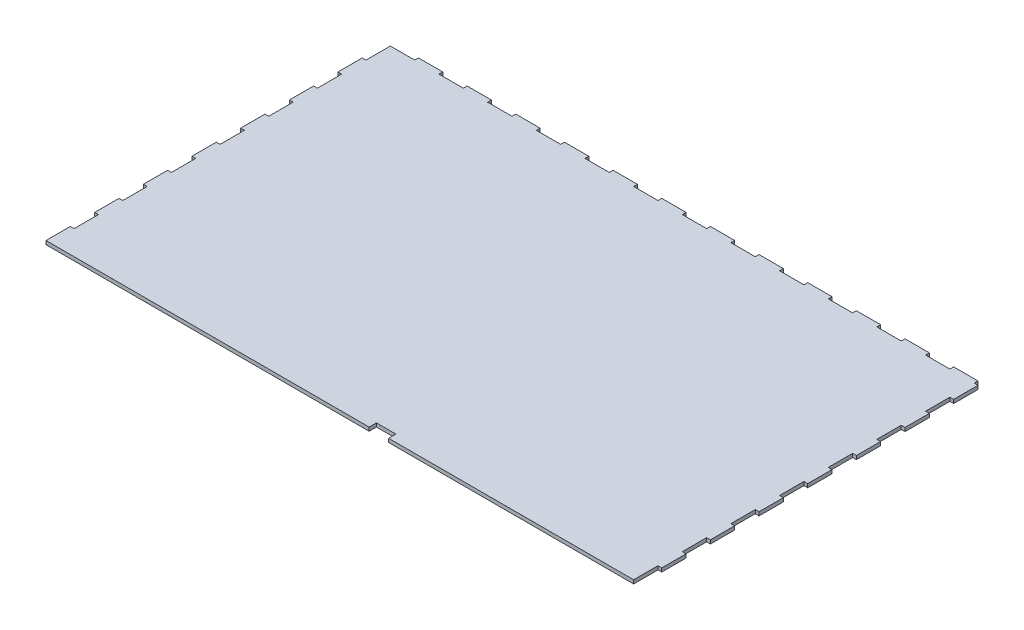
SolidWorks part; units mm, degrees
material "Acrílico (Impacto medio-alto)"
ref_plane "Alzado" through (0, 0, 0) normal (0, 0, 1) x (1, 0, 0)
ref_plane "Planta" through (0, 0, 0) normal (0, 1, 0) x (1, 0, 0)
ref_plane "Vista lateral" through (0, 0, 0) normal (1, 0, 0) x (0, 0, -1)
sketch "Croquis1" plane through (0, 0, 0) normal (0, 1, 0) x (1, 0, 0)
  line L0 (480, 280) -> (480, 283.1)
  line L1 (0, 0) -> (480, 0)
  line L2 (0, 0) -> (0, 280) construction
  line L3 (0, 280) -> (480, 280) construction
  line L4 (480, 0) -> (480, 280) construction
  line L5 (480, 283.1) -> (460, 283.1)
  line L6 (460, 283.1) -> (460, 280)
  line L7 (460, 280) -> (440, 280)
  line L8 (420, 280) -> (400, 280)
  line L9 (420, 283.1) -> (420, 280)
  line L10 (440, 283.1) -> (420, 283.1)
  line L11 (440, 280) -> (440, 283.1)
  line L12 (380, 280) -> (360, 280)
  line L13 (380, 283.1) -> (380, 280)
  line L14 (400, 283.1) -> (380, 283.1)
  line L15 (400, 280) -> (400, 283.1)
  line L16 (340, 280) -> (320, 280)
  line L17 (340, 283.1) -> (340, 280)
  line L18 (360, 283.1) -> (340, 283.1)
  line L19 (360, 280) -> (360, 283.1)
  line L20 (300, 280) -> (280, 280)
  line L21 (300, 283.1) -> (300, 280)
  line L22 (320, 283.1) -> (300, 283.1)
  line L23 (320, 280) -> (320, 283.1)
  line L24 (260, 280) -> (240, 280)
  line L25 (260, 283.1) -> (260, 280)
  line L26 (280, 283.1) -> (260, 283.1)
  line L27 (280, 280) -> (280, 283.1)
  line L28 (220, 280) -> (200, 280)
  line L29 (220, 283.1) -> (220, 280)
  line L30 (240, 283.1) -> (220, 283.1)
  line L31 (240, 280) -> (240, 283.1)
  line L32 (180, 280) -> (160, 280)
  line L33 (180, 283.1) -> (180, 280)
  line L34 (200, 283.1) -> (180, 283.1)
  line L35 (200, 280) -> (200, 283.1)
  line L36 (140, 280) -> (120, 280)
  line L37 (140, 283.1) -> (140, 280)
  line L38 (160, 283.1) -> (140, 283.1)
  line L39 (160, 280) -> (160, 283.1)
  line L40 (100, 280) -> (80, 280)
  line L41 (100, 283.1) -> (100, 280)
  line L42 (120, 283.1) -> (100, 283.1)
  line L43 (120, 280) -> (120, 283.1)
  line L44 (60, 280) -> (40, 280)
  line L45 (60, 283.1) -> (60, 280)
  line L46 (80, 283.1) -> (60, 283.1)
  line L47 (80, 280) -> (80, 283.1)
  line L48 (20, 280) -> (0, 280)
  line L49 (20, 283.1) -> (20, 280)
  line L50 (40, 283.1) -> (20, 283.1)
  line L51 (40, 280) -> (40, 283.1)
  line L52 (480, 280) -> (483.1, 280)
  line L53 (483.1, 280) -> (483.1, 260)
  line L54 (483.1, 260) -> (480, 260)
  line L55 (480, 260) -> (480, 240)
  line L56 (480, 240) -> (483.1, 240)
  line L57 (483.1, 240) -> (483.1, 220)
  line L58 (483.1, 220) -> (480, 220)
  line L59 (480, 220) -> (480, 200)
  line L60 (480, 200) -> (483.1, 200)
  line L61 (483.1, 200) -> (483.1, 180)
  line L62 (483.1, 180) -> (480, 180)
  line L63 (480, 180) -> (480, 160)
  line L64 (480, 160) -> (483.1, 160)
  line L65 (483.1, 160) -> (483.1, 140)
  line L66 (483.1, 140) -> (480, 140)
  line L67 (480, 140) -> (480, 120)
  line L68 (480, 120) -> (483.1, 120)
  line L69 (483.1, 120) -> (483.1, 100)
  line L70 (483.1, 100) -> (480, 100)
  line L71 (480, 100) -> (480, 80)
  line L72 (480, 80) -> (483.1, 80)
  line L73 (483.1, 80) -> (483.1, 60)
  line L74 (483.1, 60) -> (480, 60)
  line L75 (480, 60) -> (480, 40)
  line L76 (480, 40) -> (483.1, 40)
  line L77 (483.1, 40) -> (483.1, 20)
  line L78 (483.1, 20) -> (480, 20)
  line L79 (480, 20) -> (480, 0)
  line L80 (0, 0) -> (-3.1, 0)
  line L81 (-3.1, 0) -> (-3.1, 20)
  line L82 (-3.1, 20) -> (0, 20)
  line L83 (0, 20) -> (0, 40)
  line L84 (-3.1, 40) -> (-3.1, 60)
  line L85 (-3.1, 60) -> (0, 60)
  line L86 (0, 60) -> (0, 80)
  line L87 (0, 40) -> (-3.1, 40)
  line L88 (-3.1, 80) -> (-3.1, 100)
  line L89 (-3.1, 100) -> (0, 100)
  line L90 (0, 100) -> (0, 120)
  line L91 (0, 80) -> (-3.1, 80)
  line L92 (-3.1, 120) -> (-3.1, 140)
  line L93 (-3.1, 140) -> (0, 140)
  line L94 (0, 140) -> (0, 160)
  line L95 (0, 120) -> (-3.1, 120)
  line L96 (-3.1, 160) -> (-3.1, 180)
  line L97 (-3.1, 180) -> (0, 180)
  line L98 (0, 180) -> (0, 200)
  line L99 (0, 160) -> (-3.1, 160)
  line L100 (-3.1, 200) -> (-3.1, 220)
  line L101 (-3.1, 220) -> (0, 220)
  line L102 (0, 220) -> (0, 240)
  line L103 (0, 200) -> (-3.1, 200)
  line L104 (-3.1, 240) -> (-3.1, 260)
  line L105 (-3.1, 260) -> (0, 260)
  line L106 (0, 260) -> (0, 280)
  line L107 (0, 240) -> (-3.1, 240)
  dimension "D1" = 12
  dimension "D2" = 7
  dimension "D3" = 7
extrude "Saliente-Extruir1" add sketch "Croquis1" along normal blind 3
sketch "Croquis2" plane through (0, 3, 0) normal (0, 1, 0) x (1, 0, 0)
  line L0 (480, 0) -> (278.6, 0) construction
  line L1 (-3.1, 0) -> (480, 0) construction
  line L3 (278.6, 0) -> (262.5633, 0)
  line L4 (278.6, 0) -> (278.6, 6)
  line L5 (278.6, 6) -> (262.5633, 6)
  line L6 (262.5633, 0) -> (262.5633, 6)
extrude "Cortar-Extruir1" cut sketch "Croquis2" against normal blind 10
